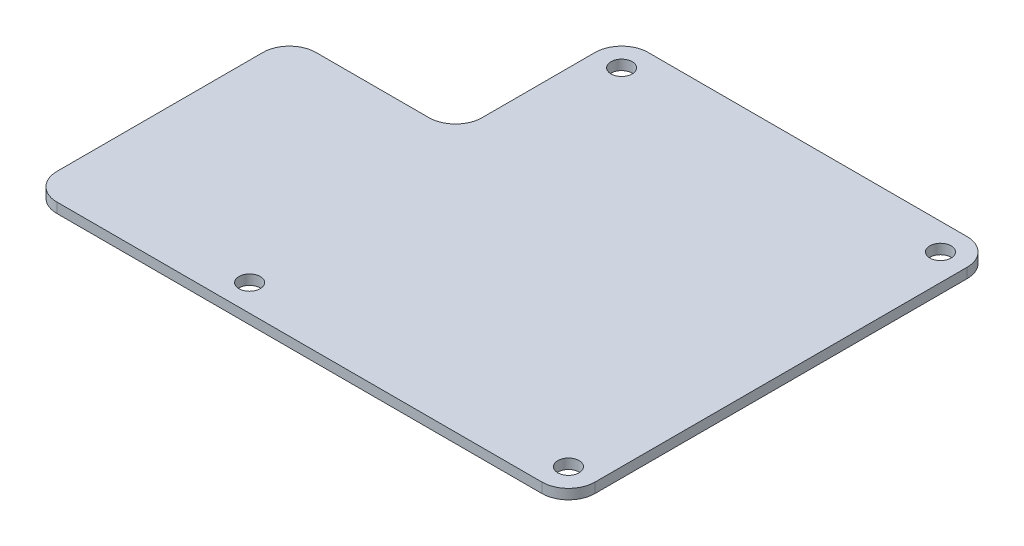
SolidWorks part; units mm, degrees
ref_plane "Front Plane" through (0, 0, 0) normal (0, 0, 1) x (1, 0, 0)
ref_plane "Top Plane" through (0, 0, 0) normal (0, 1, 0) x (1, 0, 0)
ref_plane "Right Plane" through (0, 0, 0) normal (1, 0, 0) x (0, 0, -1)
sketch "Sketch1" plane through (0, 0, 0) normal (0, 1, 0) x (1, 0, 0)
  line L0 (-8, 35) -> (-25, 35)
  line L1 (-8, -4) -> (-25, -4)
  line L2 (0, 60) -> (48, 60)
  line L3 (52, 56) -> (52, 0)
  line L4 (48, -4) -> (-8, -4)
  line L5 (-4, 39) -> (-4, 56)
  line L6 (-29, 0) -> (-29, 31)
  arc A1 (48, -4) -> (52, 0) centre (48, 0) ccw
  arc A2 (52, 56) -> (48, 60) centre (48, 56) ccw
  arc A3 (0, 60) -> (-4, 56) centre (0, 56) ccw
  circle A4 centre (0, 56) radius 1.6
  circle A5 centre (48, 56) radius 1.6
  circle A6 centre (48, 0) radius 1.6
  circle A7 centre (0, 0) radius 1.6
  arc A8 (-29, 0) -> (-25, -4) centre (-25, 0) ccw
  arc A9 (-29, 31) -> (-25, 35) centre (-25, 31) cw
  arc A10 (-8, 35) -> (-4, 39) centre (-8, 39) ccw
  dimension "D1" = 4
  dimension "D7" = 4
  dimension "D2" = 56
  dimension "D3" = 56
  dimension "D4" = 48
  dimension "D5" = 25
  dimension "D6" = 25
extrude "Boss-Extrude1" add sketch "Sketch1" along normal blind 1.5
